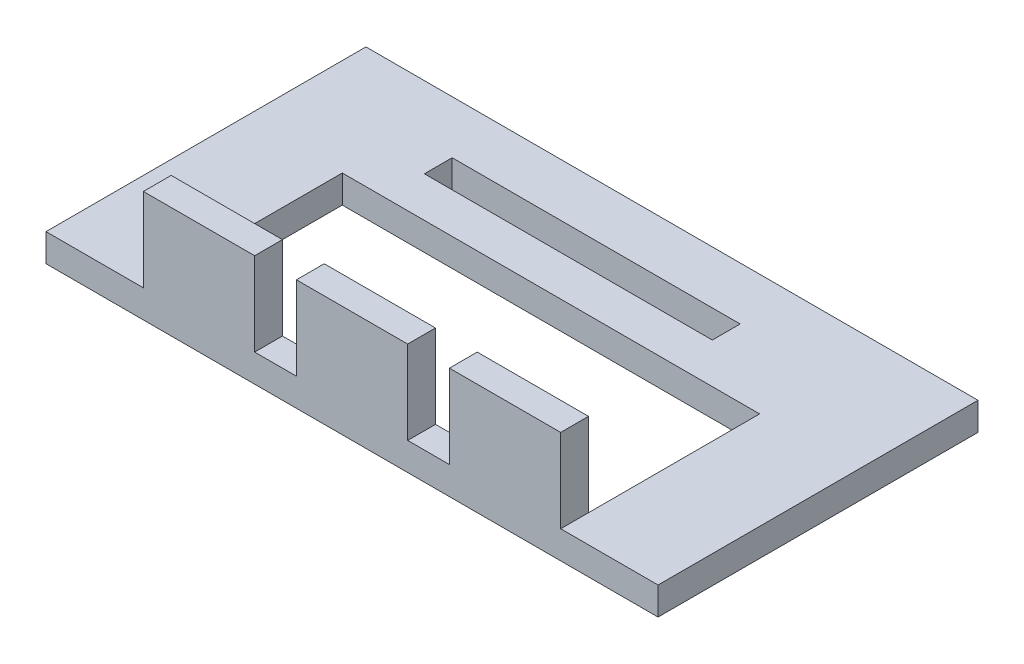
SolidWorks part; units mm, degrees
ref_plane "Front Plane" through (0, 0, 0) normal (0, 0, 1) x (1, 0, 0)
ref_plane "Top Plane" through (0, 0, 0) normal (0, 1, 0) x (1, 0, 0)
ref_plane "Right Plane" through (0, 0, 0) normal (1, 0, 0) x (0, 0, -1)
sketch "Sketch1" plane through (0, 0, 0) normal (0, 1, 0) x (1, 0, 0)
  line L1 (-22, 11.5) -> (22, 11.5)
  line L2 (-22, 11.5) -> (-22, -11.5)
  line L3 (-22, -11.5) -> (22, -11.5)
  line L4 (22, 11.5) -> (22, -11.5)
  line L5 (-22, 11.5) -> (22, -11.5) construction
  line L6 (-22, -11.5) -> (22, 11.5) construction
  point P0 (0, 0)
extrude "Boss-Extrude1" add sketch "Sketch1" along normal blind 2
sketch "Sketch2" plane through (0, 2, 0) normal (0, 1, 0) x (1, 0, 0)
  line L0 (-22, 11.5) -> (-12, 11.5) construction
  line L1 (22, 11.5) -> (-22, 11.5) construction
  line L2 (-12, 11.5) -> (-12, 5.7) construction
  line L3 (-22, -11.5) -> (-15, -11.5) construction
  line L4 (-12, 5.7) -> (8.7, 5.7)
  line L5 (-12, 5.7) -> (-12, 7.7)
  line L6 (-12, 7.7) -> (8.7, 7.7)
  line L7 (8.7, 5.7) -> (8.7, 7.7)
  line L8 (-22, -11.5) -> (22, -11.5) construction
  line L9 (-15, -11.5) -> (-15, -9.5) construction
  line L11 (-15, -9.5) -> (15, -9.5)
  line L12 (-15, -9.5) -> (-15, 2.8)
  line L13 (-15, 2.8) -> (15, 2.8)
  line L14 (15, -9.5) -> (15, 2.8)
extrude "Cut-Extrude1" cut sketch "Sketch2" against normal blind 2
sketch "Sketch3" plane through (0, 2, 0) normal (0, 1, 0) x (1, 0, 0)
  line L0 (-22, -11.5) -> (-15, -11.5) construction
  line L1 (-22, -11.5) -> (22, -11.5) construction
  line L2 (-15, -9.5) -> (15, -9.5) construction
  line L3 (-15, -11.5) -> (-7, -11.5)
  line L4 (-15, -11.5) -> (-15, -9.5)
  line L5 (-15, -9.5) -> (-7, -9.5)
  line L6 (-7, -11.5) -> (-7, -9.5)
  line L7 (-7, -11.5) -> (-4, -11.5) construction
  line L8 (4, -11.5) -> (7, -11.5) construction
  line L9 (-4, -11.5) -> (4, -11.5)
  line L10 (-4, -11.5) -> (-4, -9.5)
  line L11 (-4, -9.5) -> (4, -9.5)
  line L12 (4, -11.5) -> (4, -9.5)
  line L14 (7, -11.5) -> (15, -11.5)
  line L15 (7, -11.5) -> (7, -9.5)
  line L16 (7, -9.5) -> (15, -9.5)
  line L17 (15, -11.5) -> (15, -9.5)
extrude "Boss-Extrude2" add sketch "Sketch3" along normal blind 6
